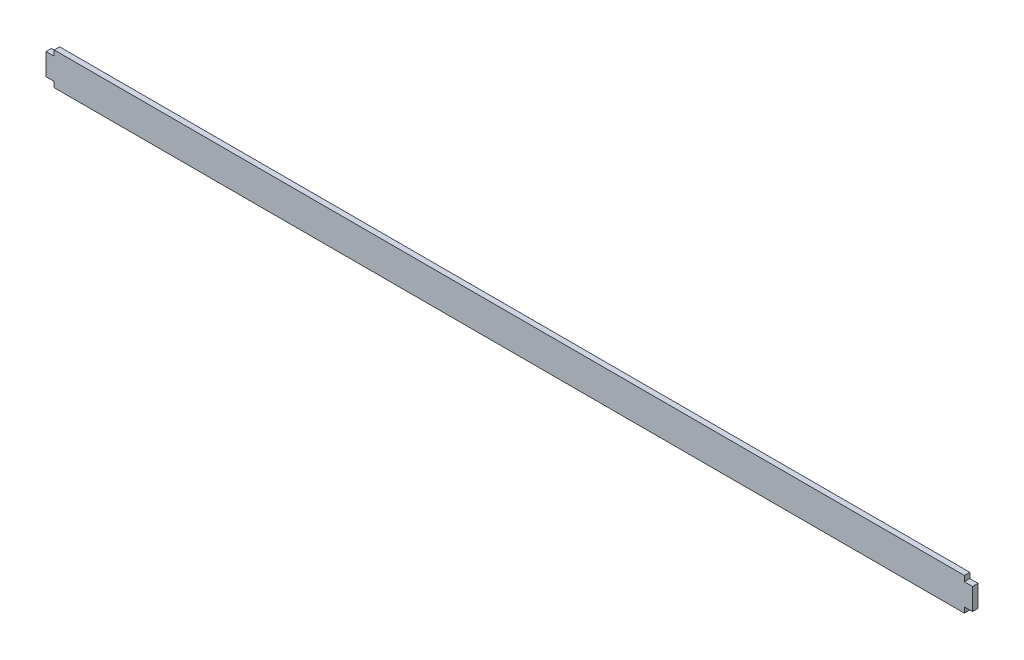
SolidWorks part; units mm, degrees
ref_plane "Front Plane" through (0, 0, 0) normal (0, 0, 1) x (1, 0, 0)
ref_plane "Top Plane" through (0, 0, 0) normal (0, 1, 0) x (1, 0, 0)
ref_plane "Right Plane" through (0, 0, 0) normal (1, 0, 0) x (0, 0, -1)
sketch "Sketch1" plane through (0, 0, 0) normal (0, 0, 1) x (1, 0, 0)
  line L0 (530.225, 15.875) -> (530.225, 19.05)
  line L1 (0, 0) -> (530.225, 0)
  line L2 (0, 0) -> (0, 3.175)
  line L3 (0, 19.05) -> (530.225, 19.05)
  line L4 (530.225, 0) -> (530.225, 3.175)
  line L5 (0, 3.175) -> (-4.7625, 3.175)
  line L7 (0, 15.875) -> (-4.7625, 15.875)
  line L8 (-4.7625, 3.175) -> (-4.7625, 15.875)
  line L13 (530.225, 3.175) -> (534.9875, 3.175)
  line L15 (530.225, 15.875) -> (534.9875, 15.875)
  line L16 (534.9875, 3.175) -> (534.9875, 15.875)
  line L17 (0, 15.875) -> (0, 19.05)
  point P10 (0, 0)
  point P12 (0, 24.349)
  point P17 (0, 25.143)
  point P18 (0, 0)
  dimension "D1" = 19.05
  dimension "D2" = 530.225
  dimension "D3" = 12.7
  dimension "D4" = 3.175
  dimension "D5" = 4.7625
  dimension "D6" = 12.7
  dimension "D7" = 4.7625
  dimension "D8" = 3.175
extrude "Boss-Extrude1" add sketch "Sketch1" along normal blind 3.175
sketch "Sketch2" plane through (0, 0, 3.175) normal (0, 0, 1) x (1, 0, 0)
  line L0 (530.225, 19.05) -> (0, 19.05) construction
  line L1 (231.2132, 19.05) -> (245.0027, 19.05)
  line L2 (231.2132, 19.05) -> (231.2132, 39.6896)
  line L4 (245.0027, 19.05) -> (245.0027, 39.6896)
  arc A0 (245.0027, 39.6896) -> (231.2132, 39.6896) centre (238.108, 39.6896) ccw
